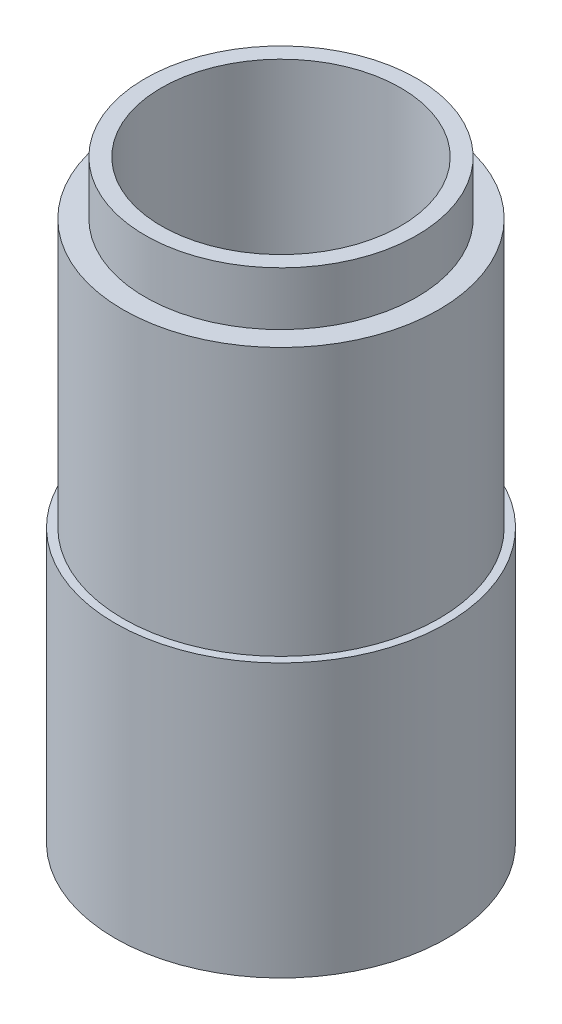
SolidWorks part; units mm, degrees
ref_plane "Front Plane" through (0, 0, 0) normal (0, 0, 1) x (1, 0, 0)
ref_plane "Top Plane" through (0, 0, 0) normal (0, 1, 0) x (1, 0, 0)
ref_plane "Right Plane" through (0, 0, 0) normal (1, 0, 0) x (0, 0, -1)
sketch "Sketch1" plane through (0, 0, 0) normal (0, 0, 1) x (1, 0, 0)
  line L0 (0, 0) -> (0, 55.5) construction
  line L2 (9.655, 0) -> (15.5, 0)
  line L3 (15.5, 0) -> (15.5, 25.5)
  line L4 (15.5, 25.5) -> (14.75, 25.5)
  line L5 (14.75, 25.5) -> (14.75, 50.5)
  line L6 (14.75, 50.5) -> (12.7, 50.5)
  line L7 (12.7, 50.5) -> (12.7, 55.5)
  line L8 (12.7, 55.5) -> (11.185, 55.5)
  line L9 (9.655, 0) -> (9.655, 5)
  line L10 (9.655, 5) -> (11.185, 5)
  line L11 (11.185, 5) -> (11.185, 55.5)
  dimension "D1" = 55.5
  dimension "D2" = 5
  dimension "D3" = 5
  dimension "D4" = 29.5
  dimension "D5" = 31
  dimension "D6" = 22.37
  dimension "D7" = 25.4
  dimension "D8" = 25
  dimension "D9" = 19.31
revolve "Revolve1" add sketch "Sketch1" angle 360 about L0
